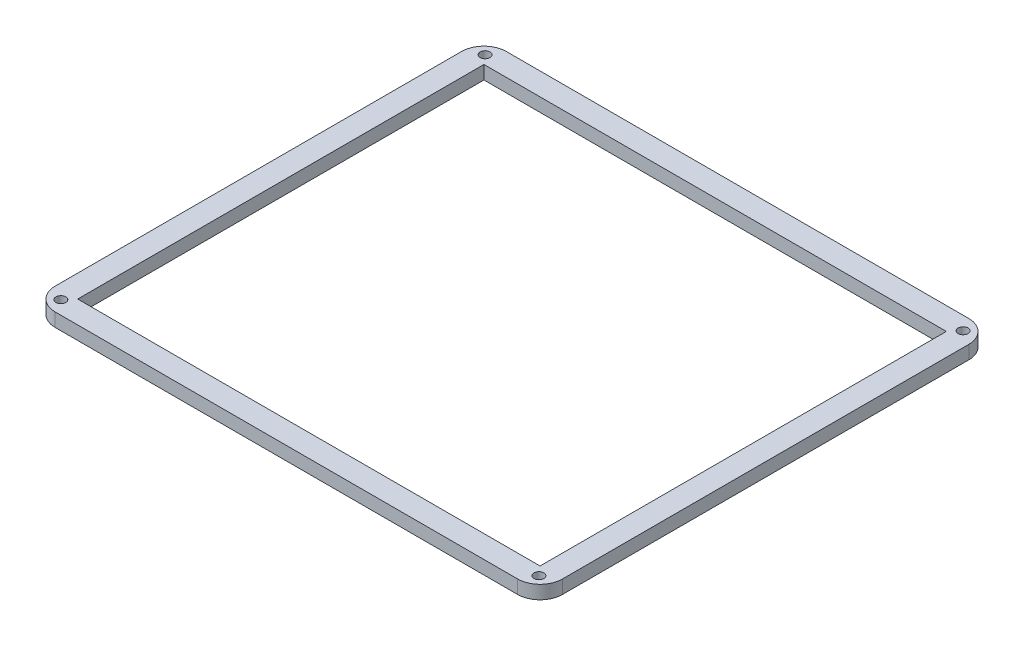
SolidWorks part; units mm, degrees
material "Acrylic (Medium-high impact)"
ref_plane "Front Plane" through (0, 0, 0) normal (0, 0, 1) x (1, 0, 0)
ref_plane "Top Plane" through (0, 0, 0) normal (0, 1, 0) x (1, 0, 0)
ref_plane "Right Plane" through (0, 0, 0) normal (1, 0, 0) x (0, 0, -1)
sketch "Sketch1" plane through (0, 0, 0) normal (0, 1, 0) x (1, 0, 0)
  line L0 (-74.707, 0) -> (86.5162, 0) construction
  line L1 (-51.5, -45.25) -> (51.5, -45.25)
  line L2 (-51.5, -45.25) -> (-51.5, 45.25)
  line L3 (-51.5, 45.25) -> (51.5, 45.25)
  line L4 (51.5, -45.25) -> (51.5, 45.25)
  line L5 (-51.5, -45.25) -> (51.5, 45.25) construction
  line L6 (-51.5, 45.25) -> (51.5, -45.25) construction
  line L7 (-51.5, -50.25) -> (51.5, -50.25)
  line L8 (-56.5, -45.25) -> (-56.5, 45.25)
  line L9 (-51.5, 50.25) -> (51.5, 50.25)
  line L10 (56.5, -45.25) -> (56.5, 45.25)
  line L11 (-56.5, -50.25) -> (56.5, 50.25) construction
  line L12 (-56.5, 50.25) -> (56.5, -50.25) construction
  line L13 (0, 81.0342) -> (0, -64.5223) construction
  line L15 (53.25, 47.25) -> (-53.25, 47.25) construction
  line L16 (53.25, 47.25) -> (53.25, -47.25) construction
  line L17 (53.25, -47.25) -> (-53.25, -47.25) construction
  line L18 (-53.25, 47.25) -> (-53.25, -47.25) construction
  line L19 (53.25, 47.25) -> (-53.25, -47.25) construction
  line L20 (53.25, -47.25) -> (-53.25, 47.25) construction
  arc A0 (-51.5, -50.25) -> (-56.5, -45.25) centre (-51.5, -45.25) cw
  arc A1 (51.5, -50.25) -> (56.5, -45.25) centre (51.5, -45.25) ccw
  arc A2 (51.5, 50.25) -> (56.5, 45.25) centre (51.5, 45.25) cw
  arc A3 (-56.5, 45.25) -> (-51.5, 50.25) centre (-51.5, 45.25) cw
  circle A4 centre (-53.25, 47.25) radius 1.1
  circle A5 centre (53.25, 47.25) radius 1.1
  circle A6 centre (53.25, -47.25) radius 1.1
  circle A7 centre (-53.25, -47.25) radius 1.1
  point P0 (0, 0)
  point P5 (0, 0)
  point P44 (0, 0)
  dimension "D5" = 5
  dimension "D6" = 106.5
  dimension "D7" = 2.2
  dimension "D1" = 103
  dimension "D2" = 90.5
  dimension "D3" = 5
  dimension "D4" = 5
  dimension "D8" = 94.5
extrude "Boss-Extrude1" add sketch "Sketch1" along normal blind 3
